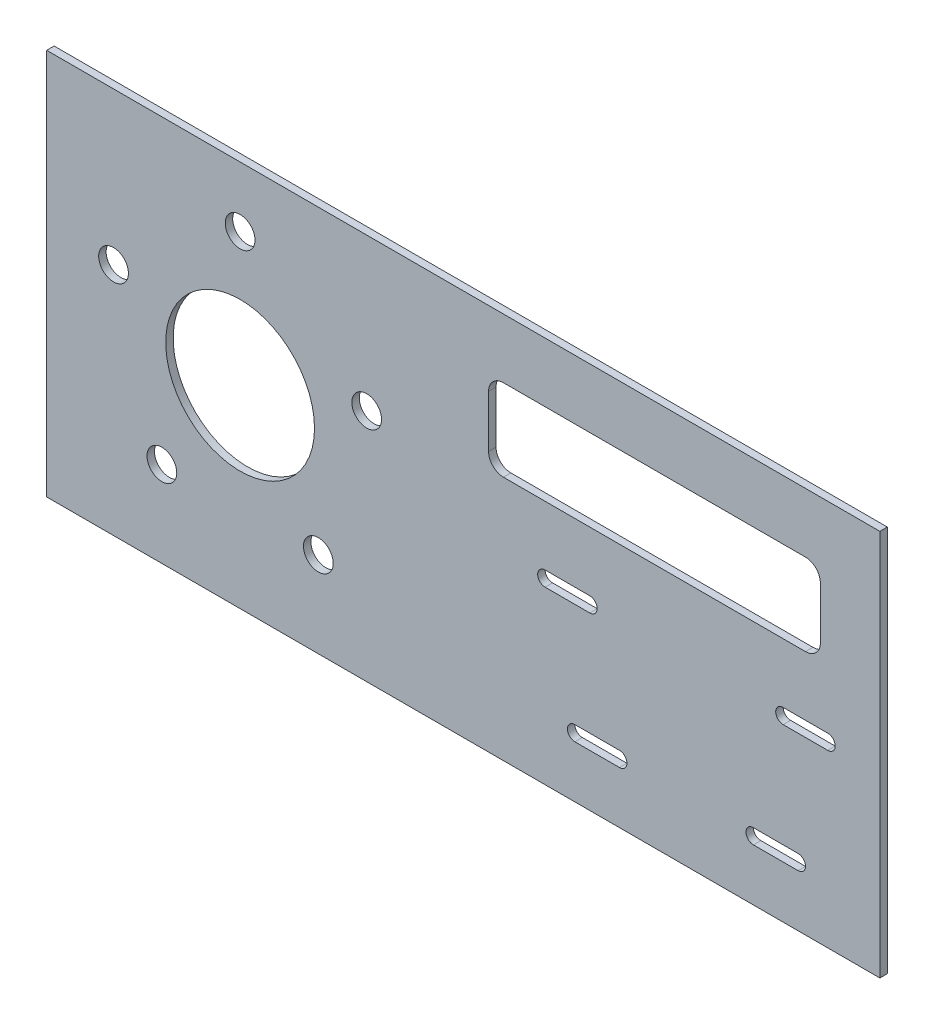
SolidWorks part; units mm, degrees
material "ASTM A36 Steel"
ref_plane "Front Plane" through (0, 0, 0) normal (0, 0, 1) x (1, 0, 0)
ref_plane "Top Plane" through (0, 0, 0) normal (0, 1, 0) x (1, 0, 0)
ref_plane "Right Plane" through (0, 0, 0) normal (1, 0, 0) x (0, 0, -1)
ref_plane "Plane1" through (190.5, 0, 0) normal (1, 0, 0) x (0, 0, -1)
sketch "Sketch1" plane through (0, 0, 0) normal (0, 0, 1) x (1, 0, 0)
  circle A2 centre (0, 0) radius 80.645
  circle A9 centre (-33.3856, -45.9513) radius 6.35
  circle A10 centre (33.3856, -45.9513) radius 6.35
  circle A11 centre (54.019, 17.5518) radius 6.35
  circle A12 centre (0, 56.7989) radius 6.35
  circle A13 centre (-54.019, 17.5518) radius 6.35
sketch "Sketch2" plane through (0, 0, 0) normal (0, 0, 1) x (1, 0, 0)
  line L0 (2.6194, 0) -> (-2.6194, 0) construction
  line L1 (273.05, -82.55) -> (-82.55, -82.55)
  line L2 (273.05, -82.55) -> (273.05, 82.55)
  line L3 (273.05, 82.55) -> (-82.55, 82.55)
  line L4 (-82.55, -82.55) -> (-82.55, 82.55)
  line L5 (273.05, -82.55) -> (-82.55, 82.55) construction
  line L6 (273.05, 82.55) -> (-82.55, -82.55) construction
  line L7 (0, -2.6194) -> (0, 2.6194) construction
  circle A0 centre (0, 0) radius 31.75
  circle A1 centre (-54.019, 17.5518) radius 6.35 construction
  circle A2 centre (0, 56.7989) radius 6.35 construction
  circle A3 centre (54.019, 17.5518) radius 6.35 construction
  circle A4 centre (33.3856, -45.9513) radius 6.35 construction
  circle A5 centre (-33.3856, -45.9513) radius 6.35 construction
  circle A6 centre (-54.019, 17.5518) radius 6.35
  circle A7 centre (0, 56.7989) radius 6.35
  circle A8 centre (54.019, 17.5518) radius 6.35
  circle A9 centre (33.3856, -45.9513) radius 6.35
  circle A10 centre (-33.3856, -45.9513) radius 6.35
  point P18 (95.25, 0)
  dimension "D1" = 63.5
  dimension "D2" = 165.1
  dimension "D3" = 82.55
  dimension "D4" = 355.6
extrude "Boss-Extrude1" add sketch "Sketch2" along normal blind 3.175
sketch "Sketch3" plane through (0, 0, 3.175) normal (0, 0, 1) x (1, 0, 0)
  line L0 (190.5, -2.6194) -> (190.5, 2.6194) construction
  line L1 (139.7, -6.35) -> (241.3, -6.35) construction
  line L2 (190.5, -6.35) -> (190.5, -57.15) construction
  line L3 (152.4, -57.15) -> (228.6, -57.15) construction
  line L4 (149.225, -6.35) -> (130.175, -6.35) construction
  line L5 (139.7, -6.35) -> (228.6, -57.15) construction
  line L6 (152.4, -57.15) -> (241.3, -6.35) construction
  line L7 (149.225, -9.525) -> (130.175, -9.525)
  line L8 (149.225, -3.175) -> (130.175, -3.175)
  line L9 (250.825, -6.35) -> (231.775, -6.35) construction
  line L10 (250.825, -9.525) -> (231.775, -9.525)
  line L11 (250.825, -3.175) -> (231.775, -3.175)
  line L12 (238.125, -57.15) -> (219.075, -57.15) construction
  line L13 (238.125, -60.325) -> (219.075, -60.325)
  line L14 (238.125, -53.975) -> (219.075, -53.975)
  line L15 (142.875, -57.15) -> (161.925, -57.15) construction
  line L16 (142.875, -53.975) -> (161.925, -53.975)
  line L17 (142.875, -60.325) -> (161.925, -60.325)
  line L18 (273.05, 82.55) -> (-82.55, 82.55) construction
  arc A0 (149.225, -9.525) -> (149.225, -3.175) centre (149.225, -6.35) ccw
  arc A1 (130.175, -3.175) -> (130.175, -9.525) centre (130.175, -6.35) ccw
  arc A2 (250.825, -9.525) -> (250.825, -3.175) centre (250.825, -6.35) ccw
  arc A3 (231.775, -3.175) -> (231.775, -9.525) centre (231.775, -6.35) ccw
  arc A4 (238.125, -60.325) -> (238.125, -53.975) centre (238.125, -57.15) ccw
  arc A5 (219.075, -53.975) -> (219.075, -60.325) centre (219.075, -57.15) ccw
  arc A6 (142.875, -53.975) -> (142.875, -60.325) centre (142.875, -57.15) ccw
  arc A7 (161.925, -60.325) -> (161.925, -53.975) centre (161.925, -57.15) ccw
  point P0 (190.5, -35.3786)
  point P11 (139.7, -6.35)
  point P18 (241.3, -6.35)
  point P23 (228.6, -57.15)
  point P30 (152.4, -57.15)
  dimension "D1" = 50.8
  dimension "D2" = 101.6
  dimension "D3" = 76.2
  dimension "D4" = 88.9
  dimension "D5" = 19.05
  dimension "D6" = 6.35
extrude "Cut-Extrude1" cut sketch "Sketch3" against normal through all
ref_plane "Plane2" through (0, -6.35, 0) normal (0, 1, 0) x (-1, 0, 0)
sketch "Sketch4" plane through (0, 0, 3.175) normal (0, 0, 1) x (1, 0, 0)
  line L0 (241.3, 57.15) -> (112.395, 57.15)
  line L1 (106.045, 50.8) -> (106.045, 28.575)
  line L2 (112.395, 22.225) -> (241.3, 22.225)
  line L3 (247.65, 28.575) -> (247.65, 50.8)
  line L4 (273.05, 82.55) -> (-82.55, 82.55) construction
  line L5 (273.05, -82.55) -> (273.05, 82.55) construction
  line L6 (149.225, -3.175) -> (130.175, -3.175) construction
  arc A0 (112.395, 57.15) -> (106.045, 50.8) centre (112.395, 50.8) ccw
  arc A1 (106.045, 28.575) -> (112.395, 22.225) centre (112.395, 28.575) ccw
  arc A2 (241.3, 22.225) -> (247.65, 28.575) centre (241.3, 28.575) ccw
  arc A3 (247.65, 50.8) -> (241.3, 57.15) centre (241.3, 50.8) ccw
  circle A5 centre (0, 0) radius 80.645 construction
  circle A6 centre (0, 0) radius 80.645
  point P21 (80.645, 0)
  dimension "D4" = 6.35
  dimension "D1" = 25.4
  dimension "D2" = 25.4
  dimension "D3" = 25.4
  dimension "D5" = 25.4
extrude "Cut-Extrude3" cut sketch "Sketch4" against normal through all contours L3 A3 L0 A0 L1 A1 L2 A2
